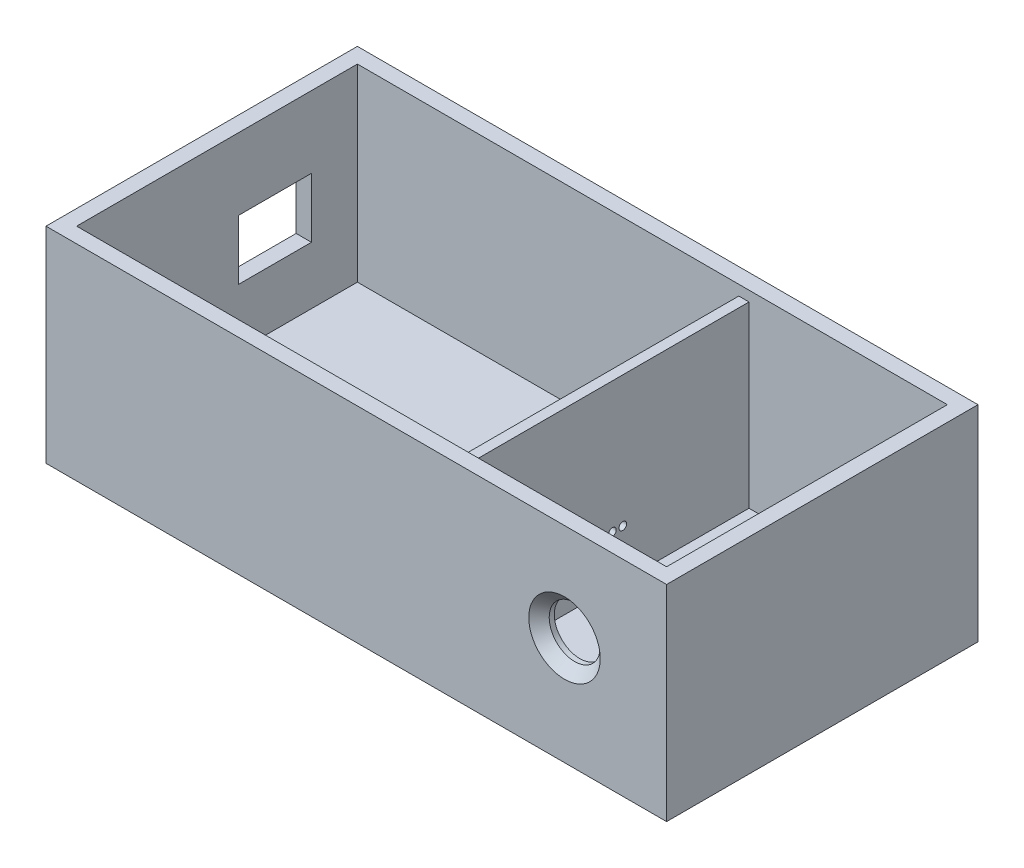
SolidWorks part; units mm, degrees
ref_plane "Front Plane" through (0, 0, 0) normal (0, 0, 1) x (1, 0, 0)
ref_plane "Top Plane" through (0, 0, 0) normal (0, 1, 0) x (1, 0, 0)
ref_plane "Right Plane" through (0, 0, 0) normal (1, 0, 0) x (0, 0, -1)
sketch "Sketch1" plane through (0, 0, 0) normal (0, 1, 0) x (1, 0, 0)
  line L1 (-60.785, 30.5) -> (60.785, 30.5)
  line L2 (-60.785, 30.5) -> (-60.785, -30.5)
  line L3 (-60.785, -30.5) -> (60.785, -30.5)
  line L4 (60.785, 30.5) -> (60.785, -30.5)
  line L5 (-60.785, 30.5) -> (60.785, -30.5) construction
  line L6 (-60.785, -30.5) -> (60.785, 30.5) construction
  point P0 (0, 0)
  dimension "D1" = 121.57
  dimension "D2" = 61
extrude "Boss-Extrude1" add sketch "Sketch1" along normal blind 3.2354
sketch "Sketch2" plane through (0, 3.2354, 0) normal (0, 1, 0) x (1, 0, 0)
  line L0 (-57.785, -27.5) -> (57.785, -27.5)
  line L1 (57.785, -27.5) -> (57.785, 27.5)
  line L2 (57.785, 27.5) -> (-57.785, 27.5)
  line L3 (-57.785, 27.5) -> (-57.785, -27.5)
  line L4 (60.785, -30.5) -> (60.785, 30.5)
  line L5 (60.785, 30.5) -> (-60.785, 30.5)
  line L6 (-60.785, 30.5) -> (-60.785, -30.5)
  line L7 (-60.785, -30.5) -> (60.785, -30.5)
  line L8 (60.785, -30.5) -> (60.785, 30.5)
  line L9 (60.785, 30.5) -> (-60.785, 30.5)
  line L10 (-60.785, 30.5) -> (-60.785, -30.5)
  line L11 (-60.785, -30.5) -> (60.785, -30.5)
  dimension "D1" = 0
  dimension "D2" = 3
extrude "Boss-Extrude2" add sketch "Sketch2" along normal blind 37
sketch "Sketch3" plane through (-60.785, 0, 0) normal (-1, 0, 0) x (0, 0, 1)
  line L0 (-30.5, 40.2354) -> (-30.5, 0) construction
  line L1 (-18.5, 14.5) -> (-4.2, 14.5)
  line L2 (-18.5, 14.5) -> (-18.5, 26.2)
  line L3 (-18.5, 26.2) -> (-4.2, 26.2)
  line L4 (-4.2, 14.5) -> (-4.2, 26.2)
  line L5 (-18.5, 14.5) -> (-4.2, 26.2) construction
  line L6 (-18.5, 26.2) -> (-4.2, 14.5) construction
  line L12 (-30.5, 0) -> (30.5, 0) construction
  point P0 (-11.35, 20.35)
  dimension "D1" = 11.7
  dimension "D2" = 12
  dimension "D3" = 34.7
  dimension "D4" = 14.5
  dimension "D6" = 14.3
extrude "Cut-Extrude1" cut sketch "Sketch3" against normal up to next
sketch "Sketch5" plane through (0, 3.2354, 0) normal (0, 1, 0) x (1, 0, 0)
  line L0 (57.785, 27.5) -> (-57.785, 27.5) construction
  line L1 (18.93, 27.5) -> (16.93, 27.5)
  line L2 (18.93, 27.5) -> (18.93, -27.5)
  line L3 (18.93, -27.5) -> (16.93, -27.5)
  line L4 (16.93, 27.5) -> (16.93, -27.5)
  line L5 (-57.785, -27.5) -> (57.785, -27.5) construction
  line L6 (16.43, 11.176) -> (16.43, -21.59) construction
  dimension "D1" = 0.5
  dimension "D2" = 2
extrude "Boss-Extrude3" add sketch "Sketch5" along normal blind 35 contours L2 L3 L4 L1
sketch "Sketch7" plane through (0, 0, 30.5) normal (0, 0, 1) x (1, 0, 0)
  line L0 (-60.785, 0) -> (60.785, 0) construction
  line L1 (60.785, 40.2354) -> (60.785, 0) construction
  circle A0 centre (40.785, 21.15) radius 5
  circle A1 centre (40.785, 21.15) radius 4
  dimension "D1" = 10
  dimension "D2" = 8
  dimension "D3" = 21.15
  dimension "D4" = 20
extrude "Cut-Extrude3" cut sketch "Sketch7" against normal blind 20
chamfer "Chamfer10" distance 2 angle 45 1 edges at (45.785, 21.15, 30.5)
sketch "Sketch8" plane through (16.93, 0, 0) normal (-1, 0, 0) x (0, 0, 1)
  circle A0 centre (-0.7371, 12.5792) radius 0.75
  circle A1 centre (1.2785, 12.5792) radius 0.75
  circle A2 centre (3.4454, 12.5792) radius 0.75
  circle A3 centre (5.7694, 12.5792) radius 0.75
  circle A4 centre (-2.7743, 12.5792) radius 0.75
  point P10 (0, 0)
  point P11 (0, 0)
  dimension "D1" = 1.5
extrude "Cut-Extrude4" cut sketch "Sketch8" against normal blind 17 and the other way blind 11
